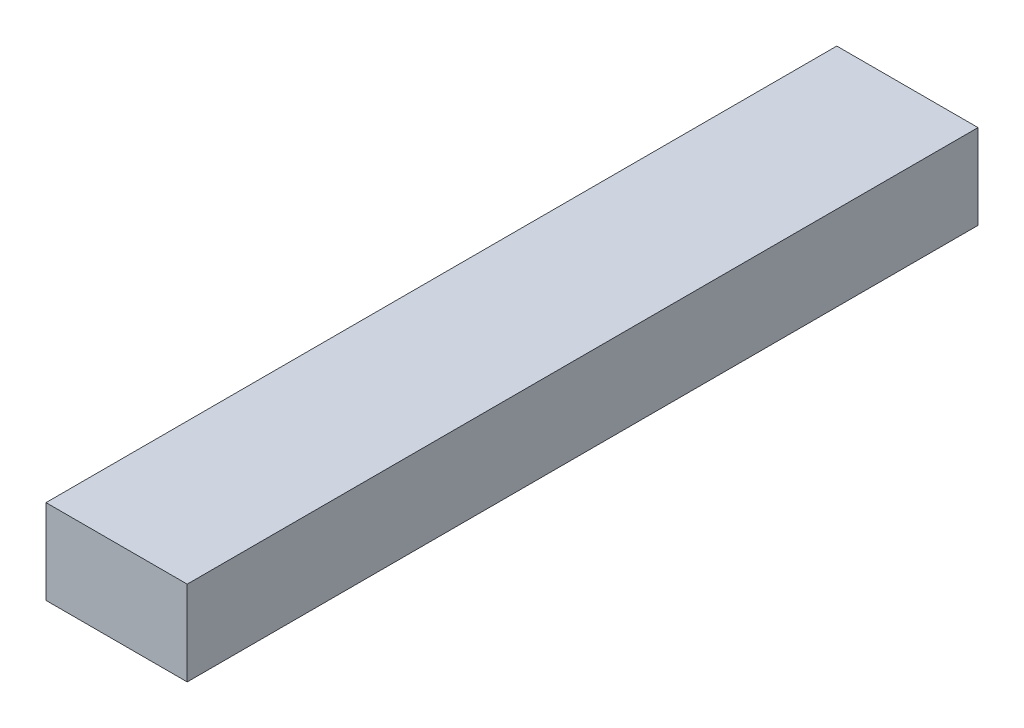
SolidWorks part; units mm, degrees
material "Alloy Steel"
ref_plane "Front Plane" through (0, 0, 0) normal (0, 0, 1) x (1, 0, 0)
ref_plane "Top Plane" through (0, 0, 0) normal (0, 1, 0) x (1, 0, 0)
ref_plane "Right Plane" through (0, 0, 0) normal (1, 0, 0) x (0, 0, -1)
sketch "Sketch1" plane through (0, 0, 0) normal (0, 1, 0) x (1, 0, 0)
  line L0 (0, 0) -> (7.9375, 0)
  line L1 (7.9375, 0) -> (7.9375, 44.45)
  line L2 (7.9375, 44.45) -> (0, 44.45)
  line L3 (0, 44.45) -> (0, 0)
  dimension "D1" = 7.9375
  dimension "D2" = 44.45
  dimension "D3" = 7.9375
extrude "Boss-Extrude1" add sketch "Sketch1" along normal blind 4.7625
